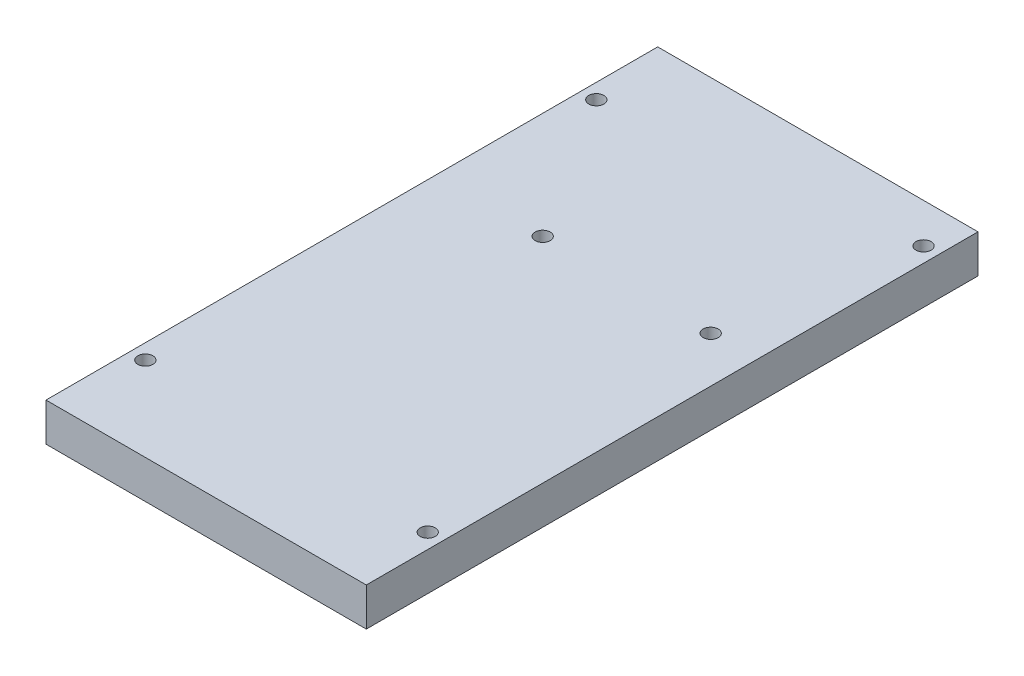
SolidWorks part; units mm, degrees
ref_plane "Front Plane" through (0, 0, 0) normal (0, 0, 1) x (1, 0, 0)
ref_plane "Top Plane" through (0, 0, 0) normal (0, 1, 0) x (1, 0, 0)
ref_plane "Right Plane" through (0, 0, 0) normal (1, 0, 0) x (0, 0, -1)
sketch "Sketch1" plane through (0, 0, 0) normal (0, 1, 0) x (1, 0, 0)
  line L0 (-50.7, 14) -> (-2.5, 14) construction
  line L1 (-2.5, 14) -> (-2.5, 12.7) construction
  line L2 (-50.7, 88.9) -> (-50.7, 14) construction
  line L3 (-2.5, 95.05) -> (-2.5, 12.7) construction
  line L4 (-35.5, 64.8) -> (-7.6, 64.8) construction
  line L5 (-53.2, 101.6) -> (0, 101.6)
  line L6 (-53.2, 101.6) -> (-53.2, 0)
  line L7 (-53.2, 0) -> (0, 0)
  line L8 (0, 101.6) -> (0, 0)
  circle A0 centre (-50.7, 88.9) radius 1.25
  circle A1 centre (-2.5, 95.05) radius 1.25
  circle A2 centre (-35.5, 64.8) radius 1.25
  circle A3 centre (-7.6, 64.8) radius 1.25
  circle A4 centre (-50.7, 14) radius 1.25
  circle A5 centre (-2.5, 12.7) radius 1.25
  dimension "D1" = 2.5
  dimension "D2" = 48.2
  dimension "D3" = 1.3
  dimension "D4" = 82.35
  dimension "D5" = 74.9
  dimension "D6" = 50.8
  dimension "D7" = 15.2
  dimension "D8" = 27.9
  dimension "D9" = 14
  dimension "D10" = 101.6
  dimension "D11" = 2.5
  dimension "D12" = 2.5
extrude "Boss-Extrude1" add sketch "Sketch1" along normal blind 6.35
